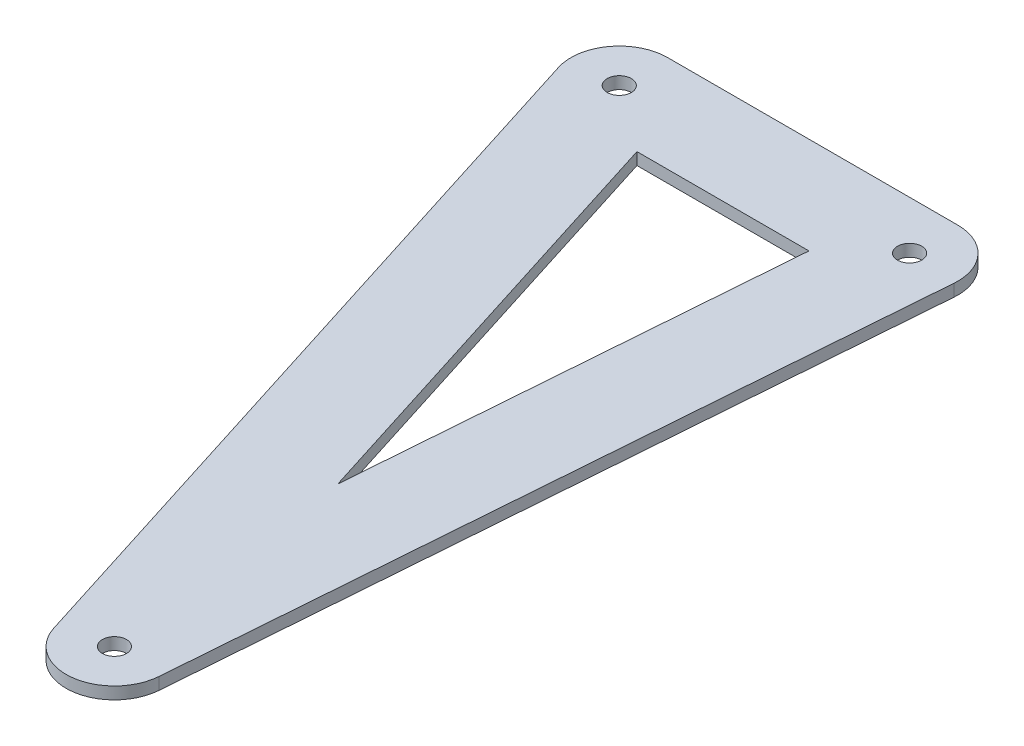
SolidWorks part; units mm, degrees
ref_plane "Front Plane" through (0, 0, 0) normal (0, 0, 1) x (1, 0, 0)
ref_plane "Top Plane" through (0, 0, 0) normal (0, 1, 0) x (1, 0, 0)
ref_plane "Right Plane" through (0, 0, 0) normal (1, 0, 0) x (0, 0, -1)
sketch "Sketch1" plane through (0, 0, 0) normal (0, 1, 0) x (1, 0, 0)
  line L0 (0, 0) -> (76.2, 0)
  line L1 (76.2, 0) -> (61.2498, -193.7491)
  line L2 (61.2498, -193.7491) -> (0, 0)
  line L3 (0, 0) -> (76.2, 0) construction
  line L4 (0, 12.7) -> (76.2, 12.7)
  line L5 (0, -12.7) -> (76.2, -12.7)
  line L6 (0, 0) -> (61.2498, -193.7491) construction
  line L7 (12.1093, 3.8281) -> (73.3591, -189.921)
  line L8 (-12.1093, -3.8281) -> (49.1405, -197.5772)
  line L9 (76.2, 0) -> (61.2498, -193.7491) construction
  line L10 (88.8624, -0.9771) -> (73.9121, -194.7261)
  line L11 (63.5376, 0.9771) -> (48.5874, -192.772)
  arc A0 (0, 12.7) -> (0, -12.7) centre (0, 0) ccw
  arc A1 (76.2, -12.7) -> (76.2, 12.7) centre (76.2, 0) ccw
  arc A2 (12.1093, 3.8281) -> (-12.1093, -3.8281) centre (0, 0) ccw
  arc A3 (49.1405, -197.5772) -> (73.3591, -189.921) centre (61.2498, -193.7491) ccw
  arc A4 (88.8624, -0.9771) -> (63.5376, 0.9771) centre (76.2, 0) ccw
  arc A5 (48.5874, -192.772) -> (73.9121, -194.7261) centre (61.2498, -193.7491) ccw
  circle A6 centre (0, 0) radius 3.175
  circle A7 centre (76.2, 0) radius 3.175
  circle A8 centre (61.2498, -193.7491) radius 3.175
  point P4 (38.1, 0)
  point P10 (30.6249, -96.8745)
  point P15 (68.7249, -96.8745)
extrude "Boss-Extrude2" add sketch "Sketch1" along normal blind 3.175 contours A5 L11 L2 L5 A0 L8 | L11 L7 L5 L2 | L7 A2 A0 L5 L2 L0 | L7 L0 L2 L5 | A4 L4 A2 L7 L0 L11 | L11 L0 L7 L5 | A1 A4 L11 L0 L1 L5 | L0 L11 L5 L1 | L5 L11 L7 L1 | A3 L10 A1 L5 L1 L7 | L11 A5 A3 L7 L1 L2 | L7 L11 L2 L1
